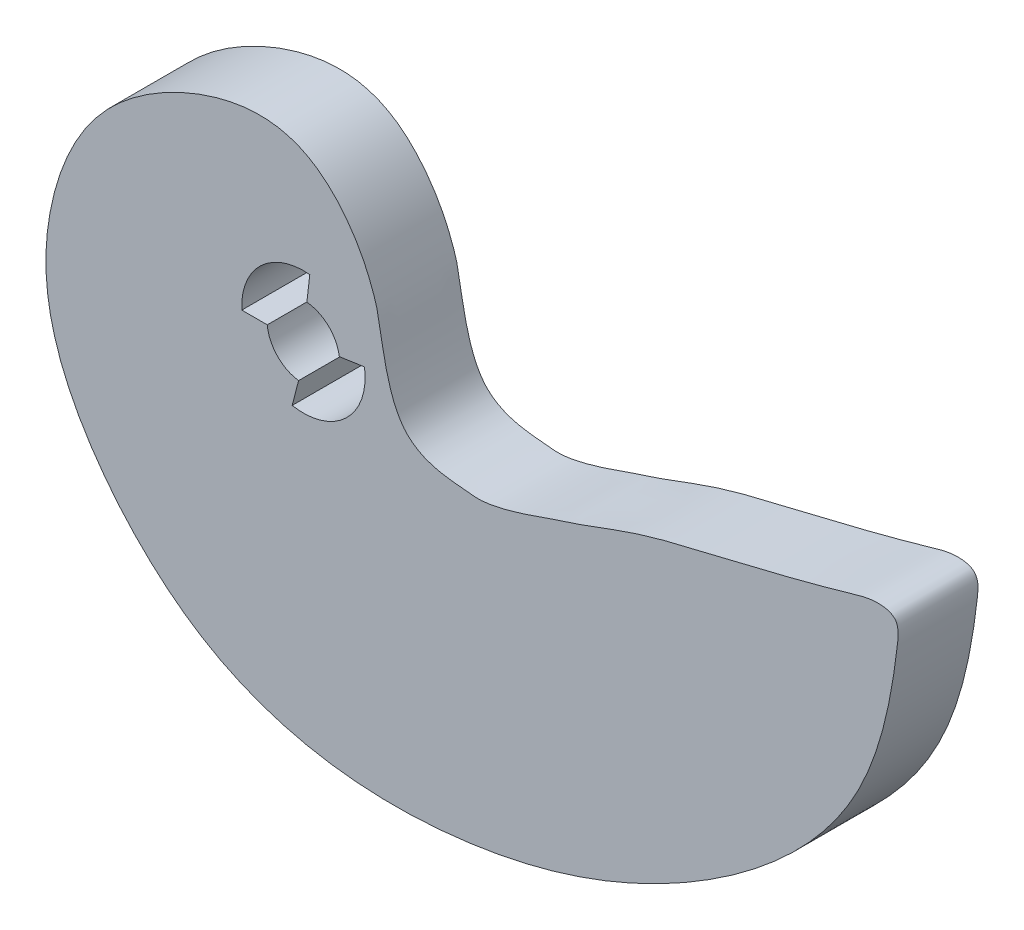
SolidWorks part; units mm, degrees
material "Acrilico (impatto medio-alto)"
ref_plane "Piano frontale" through (0, 0, 0) normal (0, 0, 1) x (1, 0, 0)
ref_plane "Piano superiore" through (0, 0, 0) normal (0, 1, 0) x (1, 0, 0)
ref_plane "Piano destro" through (0, 0, 0) normal (1, 0, 0) x (0, 0, -1)
sketch "Schizzo1" plane through (0, 0, 0) normal (0, 0, 1) x (1, 0, 0)
  line L0 (-52.9724, -29.9552) -> (143.6943, -29.9552) construction
  line L1 (-52.6572, -29.9348) -> (144.0094, -29.9348) construction
  circle A0 centre (-82.7471, -112.581) radius 2.5
  spline S0 degree 3 poles (-72.1359, -115.7576) (-76.9709, -115.6505) (-77.3807, -108.9045) (-77.8121, -107.612) (-78.3918, -105.8712) (-80.7249, -101.8414) (-85.9906, -99.1705) (-96.9079, -104.2876) (-101.0389, -113.8762) (-100.2887, -123.3028) (-89.2695, -136.5372) (-73.1959, -138.0526) (-57.4557, -133.37) (-44.6915, -123.5352) (-42.2542, -114.266) (-41.6546, -108.4806) (-43.4662, -108.2638) (-48.0536, -109.6412) (-52.3941, -110.6602) (-60.6478, -112.651) (-62.5069, -113.6121) (-64.5458, -114.2207) (-65.8452, -114.6424) (-69.5969, -116.123) (-72.1359, -115.7576) (-76.9709, -115.6505) (-77.3807, -108.9045) knots -0.045441 -0.021639 -0.016955 0 0.019605 0.020637 0.022129 0.050468 0.122903 0.200131 0.266977 0.348316 0.429985 0.551961 0.645021 0.750992 0.821689 0.830772 0.840595 0.848258 0.899741 0.910874 0.950809 0.953158 0.954559 0.978361 0.983045 1 1.019605 1.020637 1.022129 only from (-75.8242, -114.2668) to (-75.8242, -114.2668)
  point P7 (-71.985, -136.8377)
  point P9 (0, 0)
  point P10 (-58.1632, -132.6065)
  point P11 (-90.3201, -133.3117)
  point P12 (-98.8529, -123.5095)
  point P14 (-100.1223, -113.2137)
  point P16 (-96.1027, -105.3155)
  point P18 (-86.5795, -100.597)
  point P22 (-79.7728, -103.7735)
  point P26 (-64.5908, -114.2359)
  dimension "D1" = 5
extrude "Estrusione-Estrusione1" add sketch "Schizzo1" along normal blind 5.5
sketch "Schizzo2" plane through (0, 0, 5.5) normal (0, 0, 1) x (1, 0, 0)
  line L0 (-82.5092, -110.0923) -> (-82.3085, -108.3537)
  line L1 (-85.2366, -112.8097) -> (-86.9909, -112.8097)
  line L2 (-83.0804, -115.0586) -> (-83.5206, -116.76)
  line L3 (-80.2723, -112.2266) -> (-78.541, -111.9714)
  arc A0 (-83.5206, -116.76) -> (-78.541, -111.9714) centre (-82.7471, -112.581) ccw
  arc A1 (-83.0804, -115.0586) -> (-80.2723, -112.2266) centre (-82.7471, -112.581) ccw
  arc A2 (-82.5092, -110.0923) -> (-85.2366, -112.8097) centre (-82.7471, -112.581) ccw
  arc A3 (-82.3085, -108.3537) -> (-86.9909, -112.8097) centre (-82.7471, -112.581) ccw
  dimension "D1" = 5
  dimension "D2" = 8.5
extrude "Taglio-Estrusione1" cut sketch "Schizzo2" against normal blind 10 contours A1 L3 A0 L2 | A2 L1 A3 L0
equation "\"a\"= 1"
